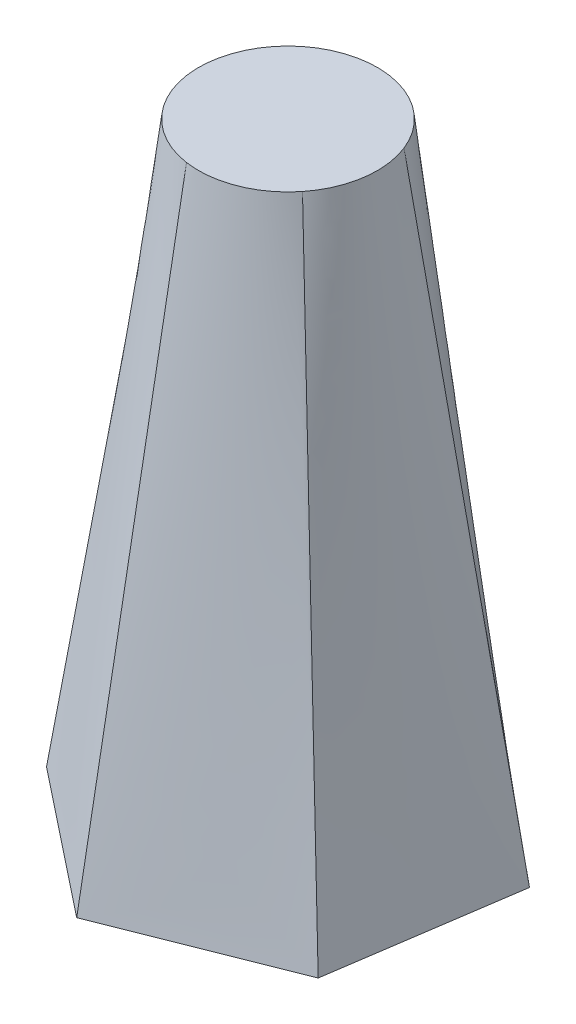
SolidWorks part; units mm, degrees
ref_plane "Front Plane" through (0, 0, 0) normal (0, 0, 1) x (1, 0, 0)
ref_plane "Top Plane" through (0, 0, 0) normal (0, 1, 0) x (1, 0, 0)
ref_plane "Right Plane" through (0, 0, 0) normal (1, 0, 0) x (0, 0, -1)
sketch "Sketch1" plane through (0, 0, 0) normal (0, 1, 0) x (1, 0, 0)
  line L1 (28.2144, 11.1631) -> (4.4397, 30.0159)
  line L2 (4.4397, 30.0159) -> (-23.7747, 18.8528)
  line L3 (-23.7747, 18.8528) -> (-28.2144, -11.1631)
  line L4 (-28.2144, -11.1631) -> (-4.4397, -30.0159)
  line L5 (-4.4397, -30.0159) -> (23.7747, -18.8528)
  line L6 (23.7747, -18.8528) -> (28.2144, 11.1631)
  circle A0 centre (0, 0) radius 26.2773 construction
ref_plane "Plane1" through (0, 100, 0) normal (0, 1, 0) x (1, 0, 0)
sketch "Sketch2" plane through (0, 100, 0) normal (0, 1, 0) x (1, 0, 0)
  circle A0 centre (0, 0) radius 14.5794
loft "Loft1" add profiles "Sketch1", "Sketch2"
